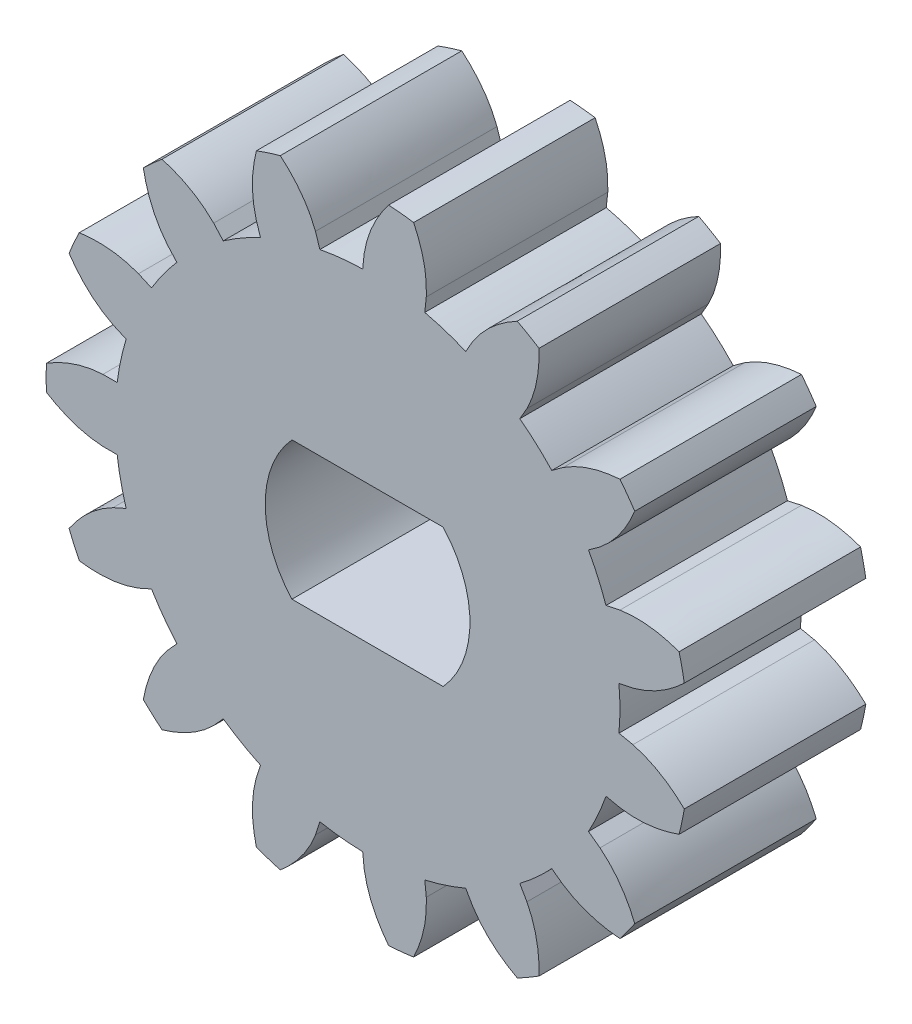
SolidWorks part; units mm, degrees
other "DetailItem2"
other "DetailItem5"
other "DetailItem6"
ref_plane "Front Plane" through (0, 0, 0) normal (0, 0, 1) x (1, 0, 0)
ref_plane "Top Plane" through (0, 0, 0) normal (0, 1, 0) x (1, 0, 0)
ref_plane "Right Plane" through (0, 0, 0) normal (1, 0, 0) x (0, 0, -1)
sketch "base_sketch" plane through (0, 0, 0) normal (0, 0, 1) x (1, 0, 0)
  line L0 (0, 0) -> (0, 7.5) construction
  line L1 (13.556, 7.5) -> (-17.4099, 7.5) construction
  line L2 (16.487, 1.4992) -> (-11.8716, 11.8209) construction
  line L3 (2.4105, 6.6227) -> (0, 0) construction
  line L4 (4.9301, 5.0363) -> (0, 0) construction
  line L5 (4.9301, 5.0363) -> (0.9532, 8.9293) construction
  line L6 (0, 0) -> (3.755, 5.9641) construction
  line L7 (3.755, 5.9641) -> (0.3149, 8.13) construction
  line L8 (5.8827, 3.8813) -> (1.9917, 9.7785) construction
  circle A0 centre (0, 0) radius 7.5 construction
  circle A1 centre (0, 0) radius 7.0477 construction
  arc A2 (2.4105, 6.6227) -> (3.755, 5.9641) centre (0, 0) cw construction
  arc A3 (3.755, 5.9641) -> (4.9301, 5.0363) centre (0, 0) cw construction
  arc A4 (4.9301, 5.0363) -> (5.8827, 3.8813) centre (0, 0) cw
  circle A5 centre (0, 0) radius 8.2262 construction
  dimension "D1" = 15
  dimension "D10" = 16.4523
  dimension "D11" = 0.4523
  dimension "D2" = 20
  dimension "D3" = 2.5652
  dimension "D4" = 1.5
  dimension "D5" = 1.5
  dimension "D6" = 5.5652
  dimension "D7" = 4.0652
  dimension "D8" = 1.5
  dimension "D9" = 7.0652
sketch "tooth" plane through (0, 0, 0) normal (0, 0, 1) x (1, 0, 0)
  line L0 (0, 0) -> (2.0705, 19.6995) construction
  line L1 (0, 0) -> (0, 7.5) construction
  line L2 (-0.0895, 7.0471) -> (-0.1289, 6.6721)
  line L4 (1.5527, 6.8745) -> (1.5133, 6.4995)
  arc A0 (0.4002, 8.4906) -> (1.3738, 8.3882) centre (0, 0) cw
  circle A1 centre (0, 0) radius 8.5 construction
  circle A2 centre (0, 0) radius 7.0477 construction
  arc A3 (-0.1289, 6.6721) -> (1.5133, 6.4995) centre (0, 0) cw
  arc A4 (0.3873, 8.217) -> (1.3295, 8.118) centre (0, 0) cw
  circle A5 centre (0, 0) radius 8.2262 construction
  spline S0 degree 3 poles (-0.0895, 7.0471) (0.098, 8.2503) (1.0493, 9.1255) (1.9917, 9.7785) knots 0 0 0 0 1 1 1 1
  spline S1 degree 3 poles (1.5527, 6.8745) (1.6195, 8.0904) (0.871, 9.1442) (0.0848, 9.9789) knots 0 0 0 0 1 1 1 1
  dimension "D2" = 17
  dimension "D1" = 6
  dimension "D3" = 0.375
sketch "Sketch12" plane through (0, 0, 0) normal (0, 0, 1) x (1, 0, 0)
  circle A0 centre (0, 0) radius 6.6734
  arc A1 (1.5133, 6.4995) -> (-0.1289, 6.6721) centre (0, 0) ccw construction
extrude "core_cyl" add sketch "Sketch12" along normal blind 4.8
extrude "tooth_ex" add sketch "tooth" along normal blind 4.8
ref_axis "Axis1" through (0, 0, 0) along (0, 0, 1)
pattern_circular "CirPattern1" count 15 over 360 about axis through (0, 0, 0) along (0, 0, 1) of "tooth_ex"
sketch "Sketch14" plane through (0, 0, 4.8) normal (0, 0, 1) x (1, 0, 0)
  circle A0 centre (0, 0) radius 2.575
  dimension "D1" = 5.15
extrude "Cut-Extrude2" [suppressed] cut sketch "Sketch14" against normal through all
sketch "Sketch13" plane through (0, 0, 4.8) normal (0, 0, 1) x (1, 0, 0)
  line L1 (-2, 1.825) -> (2, 1.825)
  line L2 (-2, 1.825) -> (-2, -1.825)
  line L3 (-2, -1.825) -> (2, -1.825)
  line L4 (2, 1.825) -> (2, -1.825)
  line L5 (-2, 1.825) -> (2, -1.825) construction
  line L6 (-2, -1.825) -> (2, 1.825) construction
  circle A0 centre (0, 0) radius 2.7075
  point P0 (0, 0)
  dimension "D1" = 3.65
  dimension "D2" = 4
extrude "Cut-Extrude1" cut sketch "Sketch13" against normal blind 4 contours L2 A0 | L4 L1 L2 L3 | L4 A0
equation "\"m\"= 1'module"
equation "\"P\"= 15'pitch diameter"
equation "\"N\"= \"P\" / \"m\"'number of teeth"
equation "\"D6@base_sketch\"=\"D5@base_sketch\"+\"D4@base_sketch\"+\"D3@base_sketch\""
equation "\"D7@base_sketch\"=\"D3@base_sketch\"+\"D4@base_sketch\""
equation "\"D1@tooth\"=360/\"N\"/4"
equation "\"D2@tooth\"=\"P\"+2*\"m\""
equation "\"D1@base_sketch\"=\"P\""
equation "\"D9@base_sketch\"=\"D6@base_sketch\"+\"D8@base_sketch\""
equation "\"D10@base_sketch\"=\"P\"+1*\"D11@base_sketch\"+1*\"m\""
